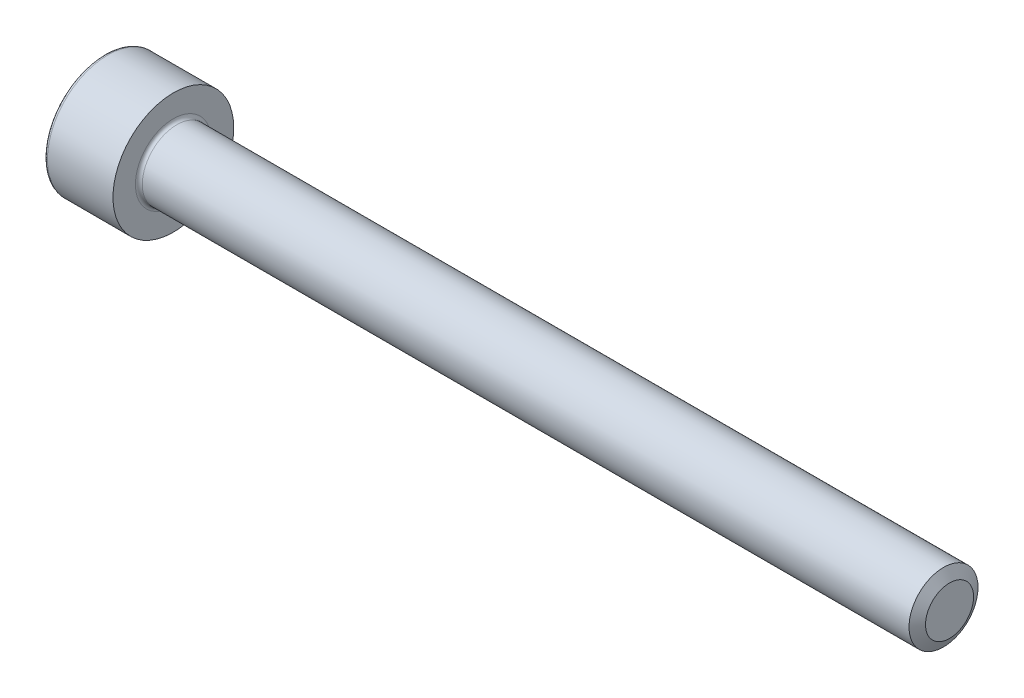
SolidWorks part; units mm, degrees
material "AISI 304"
ref_plane "前视基准面" through (0, 0, 0) normal (0, 0, 1) x (1, 0, 0)
ref_plane "上视基准面" through (0, 0, 0) normal (0, 1, 0) x (1, 0, 0)
ref_plane "右视基准面" through (0, 0, 0) normal (1, 0, 0) x (0, 0, -1)
sketch "草图1" plane through (0, 0, 0) normal (0, 0, 1) x (1, 0, 0)
  line L0 (0, 3.5) -> (0, 0)
  line L1 (0, 0) -> (4, 0)
  line L2 (4, 0) -> (4, 3.5)
  line L3 (4, 3.5) -> (0, 3.5)
  line L4 (0, 0) -> (4, 0) construction
revolve "旋转1" add sketch "草图1" angle 360 about L4
sketch "草图2" plane through (4, 0, 0) normal (1, 0, 0) x (0, 0, -1)
  circle A0 centre (0, 0) radius 2
extrude "凸台-拉伸1" add sketch "草图2" along normal blind 45
sketch "草图3" plane through (0, 0, 0) normal (-1, 0, 0) x (0, 0, 1)
  line L0 (0, 1.72) -> (-1.4896, 0.86)
  line L1 (-1.4896, 0.86) -> (-1.4896, -0.86)
  line L2 (-1.4896, -0.86) -> (0, -1.72)
  line L3 (0, -1.72) -> (1.4896, -0.86)
  line L4 (1.4896, -0.86) -> (1.4896, 0.86)
  line L5 (1.4896, 0.86) -> (0, 1.72)
extrude "切除-拉伸1" cut sketch "草图3" against normal blind 2
chamfer "倒角1" distance 0.6062 angle 30.001 1 edges at (49, 0, -2)
fillet "圆角1" radius 0.2 2 edges at (4, 0, -2) (0, 0, -3.5)
